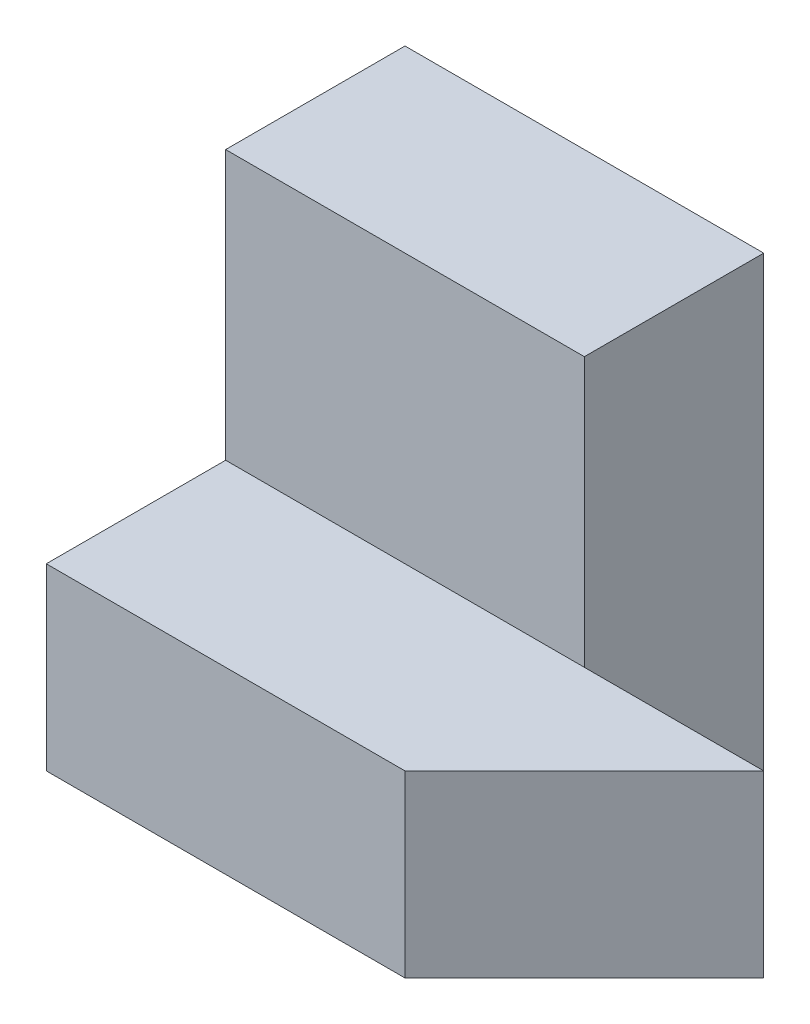
SolidWorks part; units mm, degrees
ref_plane "Front Plane" through (0, 0, 0) normal (0, 0, 1) x (1, 0, 0)
ref_plane "Top Plane" through (0, 0, 0) normal (0, 1, 0) x (1, 0, 0)
ref_plane "Right Plane" through (0, 0, 0) normal (1, 0, 0) x (0, 0, -1)
sketch "Sketch1" plane through (0, 0, 0) normal (0, 0, 1) x (1, 0, 0)
  line L1 (-2, -2.5) -> (2, -2.5)
  line L2 (-2, -2.5) -> (-2, 2.5)
  line L3 (-2, 2.5) -> (2, 2.5)
  line L4 (2, -2.5) -> (2, 2.5)
  line L5 (-2, -2.5) -> (2, 2.5) construction
  line L6 (-2, 2.5) -> (2, -2.5) construction
  point P0 (0, 0)
  dimension "D1" = 5
  dimension "D2" = 4
extrude "Boss-Extrude1" add sketch "Sketch1" along normal blind 2
sketch "Sketch2" plane through (0, 0, 2) normal (0, 0, 1) x (1, 0, 0)
  line L0 (2, -2.5) -> (2, 2.5) construction
  line L1 (-2, -2.5) -> (2, -2.5)
  line L2 (-2, -2.5) -> (-2, -0.5)
  line L3 (-2, -0.5) -> (2, -0.5)
  line L4 (2, -2.5) -> (2, -0.5)
  dimension "D1" = 2
extrude "Boss-Extrude2" add sketch "Sketch2" along normal blind 2
sketch "Sketch3" plane through (0, -0.5, 0) normal (0, 1, 0) x (1, 0, 0)
  line L0 (2, -4) -> (4, -2)
  line L1 (4, -2) -> (2, -2)
  line L2 (2, -2) -> (2, -4)
  dimension "D1" = 2
extrude "Boss-Extrude3" add sketch "Sketch3" against normal blind 2
